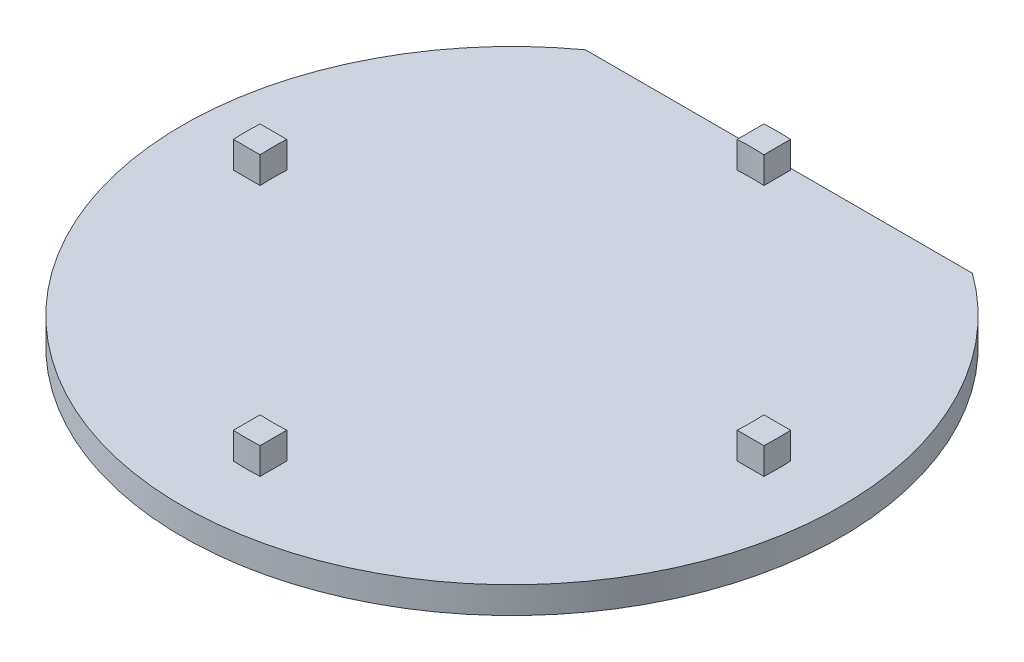
SolidWorks part; units mm, degrees
ref_plane "Front Plane" through (0, 0, 0) normal (0, 0, 1) x (1, 0, 0)
ref_plane "Top Plane" through (0, 0, 0) normal (0, 1, 0) x (1, 0, 0)
ref_plane "Right Plane" through (0, 0, 0) normal (1, 0, 0) x (0, 0, -1)
sketch "Sketch1" plane through (0, 0, 0) normal (0, 1, 0) x (1, 0, 0)
  line L1 (14.4945, 20) -> (-14.4945, 20)
  arc A0 (-14.4945, 20) -> (14.4945, 20) centre (0, 0) ccw
extrude "Boss-Extrude1" add sketch "Sketch1" along normal blind 2
sketch "Sketch2" plane through (0, 2, 0) normal (0, 1, 0) x (1, 0, 0)
  line L0 (1, 17.872) -> (1, 19.8749)
  line L1 (-1, 17.872) -> (-1, 19.8749)
  line L2 (17.872, -1) -> (19.8749, -1)
  line L3 (-17.872, -1) -> (-19.8749, -1)
  line L4 (17.872, 1) -> (19.8749, 1)
  line L5 (-17.872, 1) -> (-19.8749, 1)
  line L6 (-1, -17.872) -> (-1, -19.8749)
  line L7 (1, -17.872) -> (1, -19.8749)
  arc A0 (1, 19.8749) -> (-1, 19.8749) centre (0, 0) ccw
  arc A1 (1, 17.872) -> (-1, 17.872) centre (0, 0) ccw
  arc A2 (19.8749, -1) -> (19.8749, 1) centre (0, 0) ccw
  arc A3 (17.872, -1) -> (17.872, 1) centre (0, 0) ccw
  arc A4 (-17.872, 1) -> (-17.872, -1) centre (0, 0) ccw
  arc A5 (-19.8749, 1) -> (-19.8749, -1) centre (0, 0) ccw
  arc A6 (-1, -19.8749) -> (1, -19.8749) centre (0, 0) ccw
  arc A7 (-1, -17.872) -> (1, -17.872) centre (0, 0) ccw
  dimension "D1" = 4
extrude "Boss-Extrude2" add sketch "Sketch2" along normal blind 2
